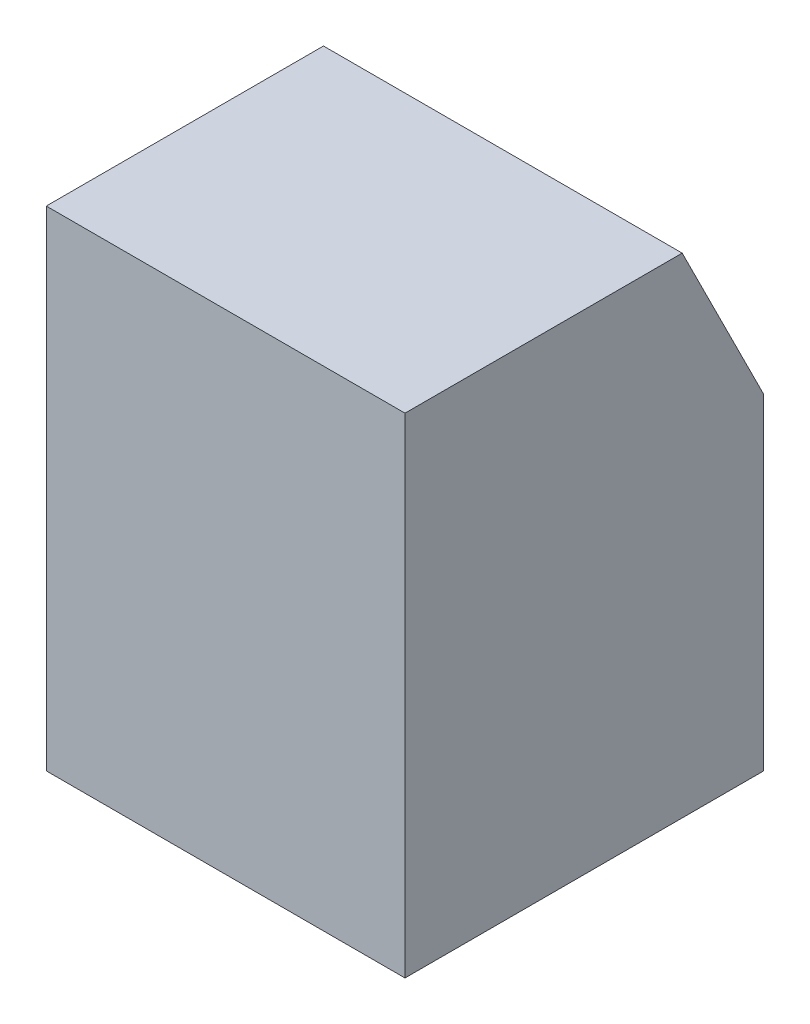
SolidWorks part; units mm, degrees
ref_plane "Front Plane" through (0, 0, 0) normal (0, 0, 1) x (1, 0, 0)
ref_plane "Top Plane" through (0, 0, 0) normal (0, 1, 0) x (1, 0, 0)
ref_plane "Right Plane" through (0, 0, 0) normal (1, 0, 0) x (0, 0, -1)
sketch "Sketch1" plane through (0, 0, 0) normal (1, 0, 0) x (0, 0, -1)
  line L0 (0, 0) -> (279.4, 0)
  line L1 (279.4, 0) -> (279.4, 254)
  line L2 (279.4, 254) -> (215.9, 381)
  line L3 (215.9, 381) -> (0, 381)
  line L4 (0, 381) -> (0, 0)
  dimension "D1" = 279.4
  dimension "D2" = 381
  dimension "D3" = 215.9
  dimension "D4" = 254
extrude "Boss-Extrude1" add sketch "Sketch1" along normal blind 279.4
sketch "Sketch2" plane through (0, 0, -279.4) normal (0, 0, -1) x (-1, 0, 0)
  line L0 (-279.4, 0) -> (0, 0) construction
  line L1 (-279.4, 0) -> (-279.4, 254) construction
  circle A0 centre (-139.7, 165.1) radius 12.7
  dimension "D1" = 25.4
  dimension "D2" = 165.1
  dimension "D3" = 139.7
extrude "Cut-Extrude1" cut sketch "Sketch2" against normal blind 127
